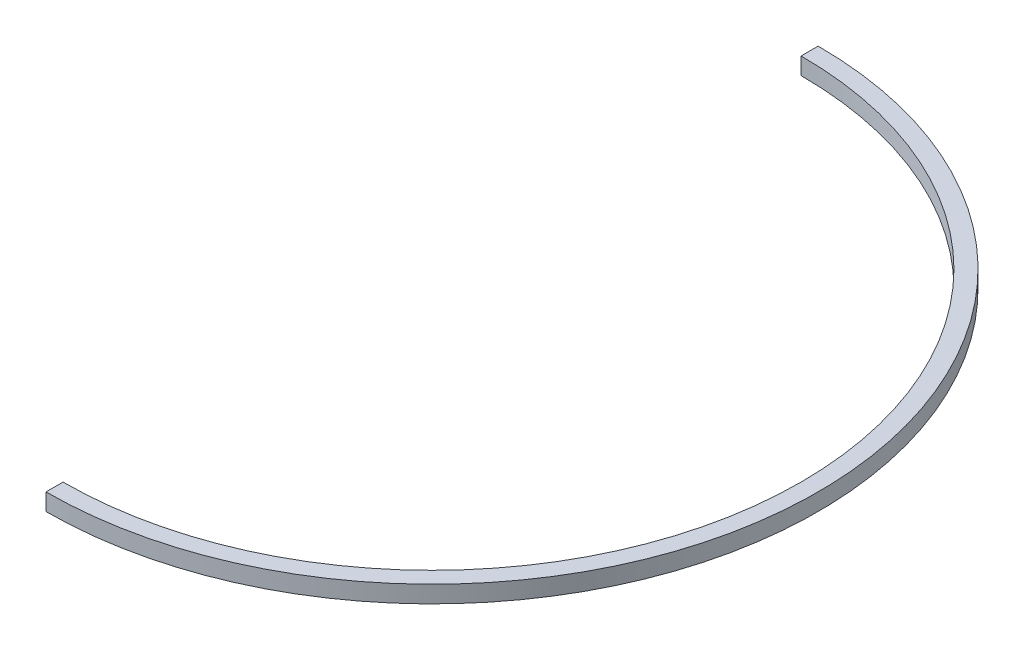
SolidWorks part; units mm, degrees
ref_plane "Płaszczyzna przednia" through (0, 0, 0) normal (0, 0, 1) x (1, 0, 0)
ref_plane "Płaszczyzna górna" through (0, 0, 0) normal (0, 1, 0) x (1, 0, 0)
ref_plane "Płaszczyzna prawa" through (0, 0, 0) normal (1, 0, 0) x (0, 0, -1)
sketch "Szkic1" plane through (0, 0, 0) normal (0, 1, 0) x (1, 0, 0)
  line L0 (0, 216.5) -> (0, 226.5)
  line L1 (0, -216.5) -> (0, -226.5)
  arc A0 (0, -226.5) -> (0, 226.5) centre (0, 0) ccw
  arc A1 (0, -216.5) -> (0, 216.5) centre (0, 0) ccw
  dimension "D1" = 453
  dimension "D2" = 433
extrude "Dodanie-wyciągnięcie1" add sketch "Szkic1" along normal blind 10
